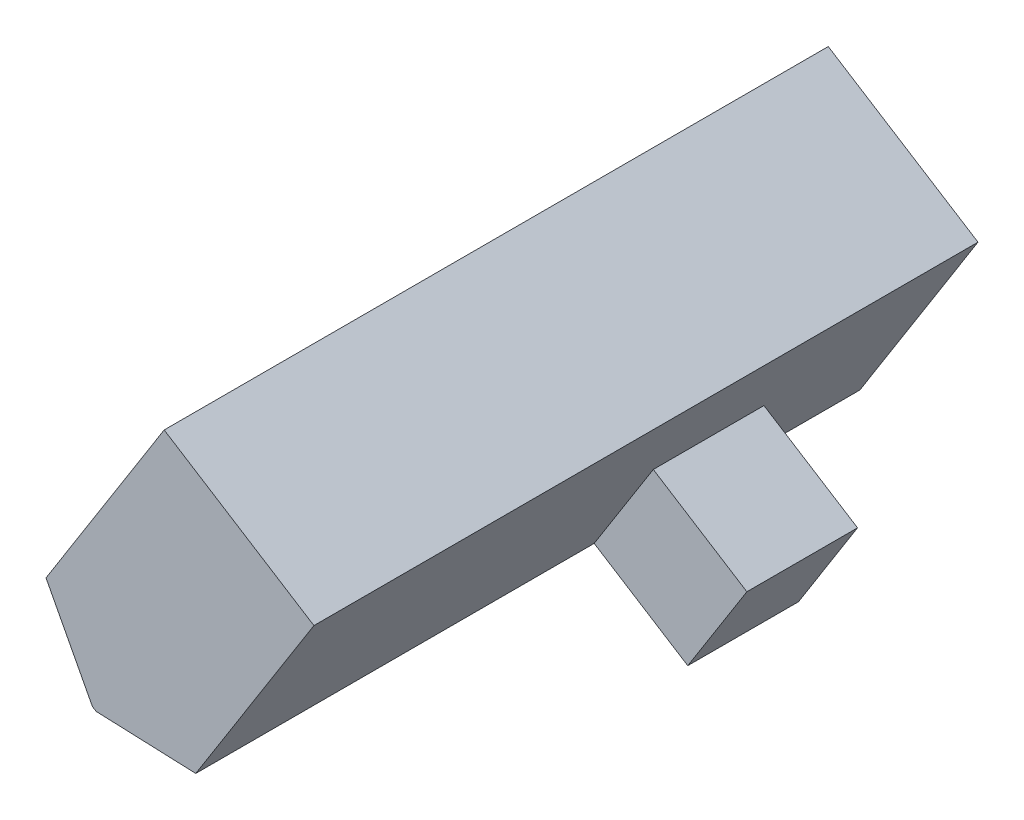
SolidWorks part; units mm, degrees
ref_plane "Front Plane" through (0, 0, 0) normal (0, 0, 1) x (1, 0, 0)
ref_plane "Top Plane" through (0, 0, 0) normal (0, 1, 0) x (1, 0, 0)
ref_plane "Right Plane" through (0, 0, 0) normal (1, 0, 0) x (0, 0, -1)
sketch "Sketch2" plane through (0, 0, 0) normal (0, 0, 1) x (1, 0, 0)
  line L1 (16.8263, 24.0268) -> (14.731, 28.0125)
  line L2 (16.996, 23.9196) -> (21.4954, 23.7413)
  line L3 (16.8263, 24.0268) -> (16.996, 23.9196)
  line L4 (14.731, 28.0125) -> (21.4954, 23.7413)
  dimension "D1" = 120
  dimension "D2" = 150
  dimension "D3" = 8
extrude "Boss-Extrude2" add sketch "Sketch2" along normal blind 30
sketch "Sketch3" plane through (16.845, 26.6777, 0) normal (0.5339, 0.8455, 0) x (0.8455, -0.5339, 0)
  line L0 (5.4998, -30) -> (-2.5002, -30) construction
  line L1 (5.4998, 0) -> (-2.5002, 0) construction
  line L2 (5.4998, -30) -> (5.4998, 0) construction
  line L3 (-2.5002, -30) -> (-2.5002, 0) construction
  line L4 (5.4998, -30) -> (-2.5002, -30)
  line L5 (5.4998, 0) -> (-2.5002, 0)
  line L6 (5.4998, -30) -> (5.4998, 0)
  line L7 (-2.5002, -30) -> (-2.5002, 0)
extrude "Boss-Extrude3" add sketch "Sketch3" along normal blind 10
sketch "Sketch5" plane through (0, 0, 30) normal (0, 0, 1) x (1, 0, 0)
  line L0 (24.1649, 27.969) -> (28.3926, 25.2995)
  line L1 (26.8344, 32.1968) -> (21.4954, 23.7413) construction
  line L2 (25.7231, 21.0718) -> (28.3926, 25.2995)
  line L3 (25.7231, 21.0718) -> (21.4954, 23.7413)
  line L4 (21.4954, 23.7413) -> (24.1649, 27.969)
  dimension "D1" = 5
  dimension "D2" = 5
  dimension "D3" = 5
  dimension "D4" = 0
extrude "Boss-Extrude4" add sketch "Sketch5" against normal blind 23
sketch "Sketch6" plane through (0, 0, 30) normal (0, 0, 1) x (1, 0, 0)
  line L0 (21.4954, 23.7413) -> (24.1649, 27.969)
  line L1 (21.4954, 23.7413) -> (25.7231, 21.0718) construction
  line L2 (25.7231, 21.0718) -> (28.3926, 25.2995) construction
  line L3 (28.3926, 25.2995) -> (24.1649, 27.969) construction
  line L4 (21.4954, 23.7413) -> (25.7231, 21.0718)
  line L5 (25.7231, 21.0718) -> (28.3926, 25.2995)
  line L6 (28.3926, 25.2995) -> (24.1649, 27.969)
extrude "Cut-Extrude1" cut sketch "Sketch6" against normal blind 18
